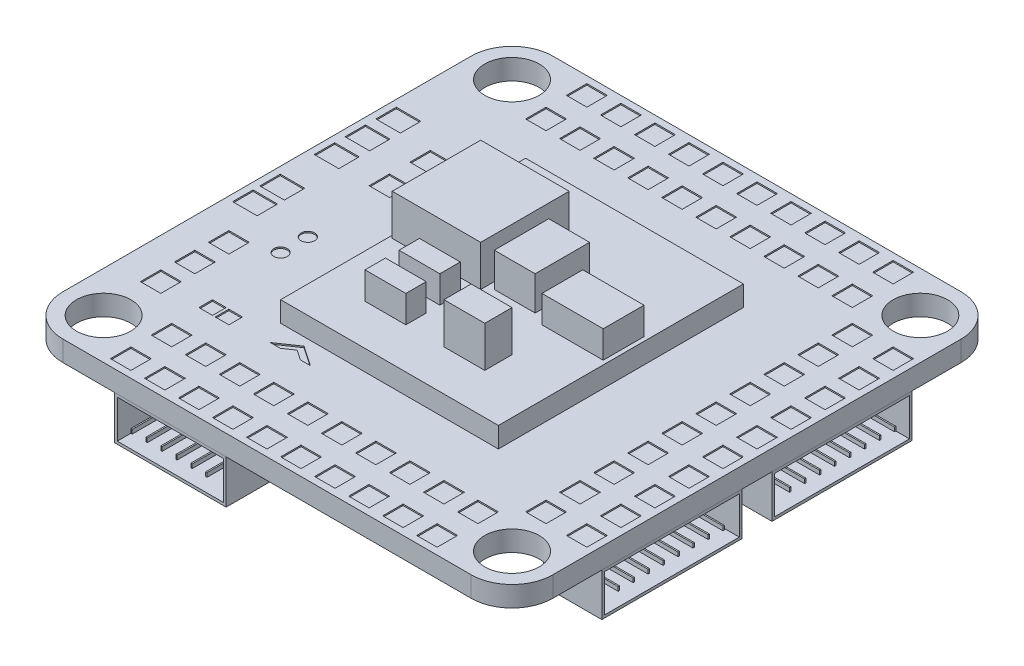
SolidWorks part; units mm, degrees
ref_plane "Front Plane" through (0, 0, 0) normal (0, 0, 1) x (1, 0, 0)
ref_plane "Top Plane" through (0, 0, 0) normal (0, 1, 0) x (1, 0, 0)
ref_plane "Right Plane" through (0, 0, 0) normal (1, 0, 0) x (0, 0, -1)
sketch "Sketch1" plane through (0, 0, 0) normal (0, 1, 0) x (1, 0, 0)
  line L1 (-15, 18) -> (15, 18)
  line L2 (-18, 15) -> (-18, -15)
  line L3 (-15, -18) -> (15, -18)
  line L4 (18, 15) -> (18, -15)
  line L5 (-18, 18) -> (18, -18) construction
  line L6 (-18, -18) -> (18, 18) construction
  circle A0 centre (-15, 15) radius 2
  circle A1 centre (15, 15) radius 2
  circle A2 centre (15, -15) radius 2
  circle A3 centre (-15, -15) radius 2
  arc A4 (-18, -15) -> (-15, -18) centre (-15, -15) ccw
  arc A5 (15, -18) -> (18, -15) centre (15, -15) ccw
  arc A6 (15, 18) -> (18, 15) centre (15, 15) cw
  arc A7 (-18, 15) -> (-15, 18) centre (-15, 15) cw
  point P0 (0, 0)
  dimension "D3" = 4
  dimension "D4" = 3
  dimension "D5" = 3
  dimension "D8" = 30
  dimension "D9" = 30
  dimension "D10" = 3
  dimension "D1" = 36
  dimension "D2" = 36
  dimension "D6" = 2
  dimension "D7" = 2
extrude "Boss-Extrude1" add sketch "Sketch1" along normal blind 1.5
sketch "Sketch2" plane through (0, 1.5, 0) normal (0, 1, 0) x (1, 0, 0)
  line L1 (-8, 9) -> (8, 9)
  line L2 (-8, 9) -> (-8, -9)
  line L3 (-8, -9) -> (8, -9)
  line L4 (8, 9) -> (8, -9)
  line L5 (-8, 9) -> (8, -9) construction
  line L6 (-8, -9) -> (8, 9) construction
  point P0 (0, 0)
  dimension "D1" = 16
  dimension "D2" = 18
extrude "Boss-Extrude2" add sketch "Sketch2" along normal blind 1.5
sketch "Sketch3" plane through (0, 3, 0) normal (0, 1, 0) x (1, 0, 0)
  line L0 (8, 9) -> (-8, 9) construction
  line L1 (-7.8, 5.5) -> (-1.3, 5.5)
  line L2 (-7.8, 5.5) -> (-7.8, -1)
  line L3 (-7.8, -1) -> (-1.3, -1)
  line L4 (-1.3, 5.5) -> (-1.3, -1)
  line L5 (-7.8, 5.5) -> (-1.3, -1) construction
  line L6 (-7.8, -1) -> (-1.3, 5.5) construction
  line L7 (8, -9) -> (8, 9) construction
  point P0 (-4.55, 2.25)
  dimension "D1" = 6.5
  dimension "D2" = 6.5
  dimension "D3" = 3.5
  dimension "D4" = 9.3
extrude "Boss-Extrude3" add sketch "Sketch3" along normal blind 3
sketch "Sketch4" plane through (0, 3, 0) normal (0, 1, 0) x (1, 0, 0)
  line L0 (-7.8, -1) -> (-1.3, -1) construction
  line L1 (-4.8, -2) -> (-1.8, -2)
  line L2 (-4.8, -2) -> (-4.8, -3.5)
  line L3 (-4.8, -3.5) -> (-1.8, -3.5)
  line L4 (-1.8, -2) -> (-1.8, -3.5)
  line L5 (-4.8, -2) -> (-1.8, -3.5) construction
  line L6 (-4.8, -3.5) -> (-1.8, -2) construction
  line L7 (-1.3, -1) -> (-1.3, 5.5) construction
  line L8 (-4.8, -4.5) -> (-4.8, -6)
  line L9 (-4.8, -4.5) -> (-1.8, -4.5)
  line L10 (-1.8, -4.5) -> (-1.8, -6)
  line L11 (-4.8, -6) -> (-1.8, -6)
  point P0 (-3.3, -2.75)
  dimension "D1" = 1.5
  dimension "D2" = 3
  dimension "D3" = 1
  dimension "D4" = 0.5
  dimension "D5" = 2
extrude "Boss-Extrude4" add sketch "Sketch4" along normal blind 2
sketch "Sketch5" plane through (0, 3, 0) normal (0, 1, 0) x (1, 0, 0)
  line L0 (8, -9) -> (8, 9) construction
  line L1 (1, -4) -> (4, -4)
  line L2 (1, -4) -> (1, -6)
  line L3 (1, -6) -> (4, -6)
  line L4 (4, -4) -> (4, -6)
  line L5 (1, -4) -> (4, -6) construction
  line L6 (1, -6) -> (4, -4) construction
  line L7 (-8, -9) -> (8, -9) construction
  point P0 (2.5, -5)
  dimension "D1" = 2
  dimension "D2" = 3
  dimension "D3" = 4
  dimension "D4" = 3
extrude "Boss-Extrude5" add sketch "Sketch5" along normal blind 3
sketch "Sketch6" plane through (0, 3, 0) normal (0, 1, 0) x (1, 0, 0)
  line L0 (-1.3, -1) -> (-1.3, 5.5) construction
  line L1 (-0.8, 3.5) -> (2.2, 3.5)
  line L2 (-0.8, 3.5) -> (-0.8, -0.5)
  line L3 (-0.8, -0.5) -> (2.2, -0.5)
  line L4 (2.2, 3.5) -> (2.2, -0.5)
  line L5 (-0.8, 3.5) -> (2.2, -0.5) construction
  line L6 (-0.8, -0.5) -> (2.2, 3.5) construction
  line L8 (-7.8, -1) -> (-1.3, -1) construction
  point P0 (0.7, 1.5)
  dimension "D1" = 4
  dimension "D2" = 3
  dimension "D3" = 0.5
  dimension "D4" = 0.5
extrude "Boss-Extrude6" add sketch "Sketch6" along normal blind 2.5
sketch "Sketch7" plane through (0, 3, 0) normal (0, 1, 0) x (1, 0, 0)
  line L0 (8, -9) -> (8, 9) construction
  line L1 (3.2, 2) -> (7.7, 2)
  line L2 (3.2, 2) -> (3.2, -1)
  line L3 (3.2, -1) -> (7.7, -1)
  line L4 (7.7, 2) -> (7.7, -1)
  line L5 (3.2, 2) -> (7.7, -1) construction
  line L6 (3.2, -1) -> (7.7, 2) construction
  line L7 (8, 9) -> (-8, 9) construction
  point P0 (5.45, 0.5)
  dimension "D1" = 4.5
  dimension "D2" = 3
  dimension "D3" = 0.3
  dimension "D4" = 7
extrude "Boss-Extrude7" add sketch "Sketch7" along normal blind 2
sketch "Sketch8" plane through (0, 1.5, 0) normal (0, 1, 0) x (1, 0, 0)
  line L0 (-5.6809, -9.5944) -> (-7.1537, -10.6043)
  line L1 (-7.1537, -10.6043) -> (-6.4173, -10.6043)
  line L2 (-6.4173, -10.6043) -> (-5.6809, -10.0993)
  line L3 (-5.6809, -9.5944) -> (-5.6809, -10.6043) construction
  line L4 (-4.9445, -10.6043) -> (-5.6809, -10.0993)
  line L5 (-4.2081, -10.6043) -> (-4.9445, -10.6043)
  line L6 (-5.6809, -9.5944) -> (-4.2081, -10.6043)
extrude "Cut-Extrude1" cut sketch "Sketch8" against normal blind 0.1
sketch "Sketch9" plane through (0, 1.5, 0) normal (0, 1, 0) x (1, 0, 0)
  line L0 (-18, 15) -> (-18, -15) construction
  line L1 (-12, -13) -> (-10.5, -13)
  line L2 (-12, -13) -> (-12, -14.5)
  line L3 (-12, -14.5) -> (-10.5, -14.5)
  line L4 (-10.5, -13) -> (-10.5, -14.5)
  line L5 (-12, -13) -> (-10.5, -14.5) construction
  line L6 (-12, -14.5) -> (-10.5, -13) construction
  line L7 (-15, -18) -> (15, -18) construction
  line L8 (-9.5, -13) -> (-9.5, -14.5)
  line L9 (-9.5, -13) -> (-8, -13)
  line L10 (-8, -13) -> (-8, -14.5)
  line L11 (-9.5, -14.5) -> (-8, -14.5)
  line L12 (-7, -13) -> (-7, -14.5)
  line L13 (-7, -13) -> (-5.5, -13)
  line L14 (-5.5, -13) -> (-5.5, -14.5)
  line L15 (-7, -14.5) -> (-5.5, -14.5)
  line L16 (-4.5, -13) -> (-4.5, -14.5)
  line L17 (-4.5, -13) -> (-3, -13)
  line L18 (-3, -13) -> (-3, -14.5)
  line L19 (-4.5, -14.5) -> (-3, -14.5)
  line L20 (-2, -13) -> (-2, -14.5)
  line L21 (-2, -13) -> (-0.5, -13)
  line L22 (-0.5, -13) -> (-0.5, -14.5)
  line L23 (-2, -14.5) -> (-0.5, -14.5)
  line L24 (0.5, -13) -> (0.5, -14.5)
  line L25 (0.5, -13) -> (2, -13)
  line L26 (2, -13) -> (2, -14.5)
  line L27 (0.5, -14.5) -> (2, -14.5)
  line L28 (3, -13) -> (3, -14.5)
  line L29 (3, -13) -> (4.5, -13)
  line L30 (4.5, -13) -> (4.5, -14.5)
  line L31 (3, -14.5) -> (4.5, -14.5)
  line L32 (5.5, -13) -> (5.5, -14.5)
  line L33 (5.5, -13) -> (7, -13)
  line L34 (7, -13) -> (7, -14.5)
  line L35 (5.5, -14.5) -> (7, -14.5)
  line L36 (8, -13) -> (8, -14.5)
  line L37 (8, -13) -> (9.5, -13)
  line L38 (9.5, -13) -> (9.5, -14.5)
  line L39 (8, -14.5) -> (9.5, -14.5)
  line L40 (10.5, -13) -> (10.5, -14.5)
  line L41 (10.5, -13) -> (12, -13)
  line L42 (12, -13) -> (12, -14.5)
  line L43 (10.5, -14.5) -> (12, -14.5)
  line L44 (-9.5, -16) -> (-9.5, -17.5)
  line L45 (-9.5, -16) -> (-8, -16)
  line L46 (-8, -16) -> (-8, -17.5)
  line L47 (-9.5, -17.5) -> (-8, -17.5)
  line L48 (-7, -16) -> (-7, -17.5)
  line L49 (-7, -16) -> (-5.5, -16)
  line L50 (-5.5, -16) -> (-5.5, -17.5)
  line L51 (-7, -17.5) -> (-5.5, -17.5)
  line L52 (-4.5, -16) -> (-4.5, -17.5)
  line L53 (-4.5, -16) -> (-3, -16)
  line L54 (-3, -16) -> (-3, -17.5)
  line L55 (-4.5, -17.5) -> (-3, -17.5)
  line L56 (-2, -16) -> (-2, -17.5)
  line L57 (-2, -16) -> (-0.5, -16)
  line L58 (-0.5, -16) -> (-0.5, -17.5)
  line L59 (-2, -17.5) -> (-0.5, -17.5)
  line L60 (0.5, -16) -> (0.5, -17.5)
  line L61 (0.5, -16) -> (2, -16)
  line L62 (2, -16) -> (2, -17.5)
  line L63 (0.5, -17.5) -> (2, -17.5)
  line L64 (3, -16) -> (3, -17.5)
  line L65 (3, -16) -> (4.5, -16)
  line L66 (4.5, -16) -> (4.5, -17.5)
  line L67 (3, -17.5) -> (4.5, -17.5)
  line L68 (5.5, -16) -> (5.5, -17.5)
  line L69 (5.5, -16) -> (7, -16)
  line L70 (7, -16) -> (7, -17.5)
  line L71 (5.5, -17.5) -> (7, -17.5)
  line L72 (8, -16) -> (8, -17.5)
  line L73 (8, -16) -> (9.5, -16)
  line L74 (9.5, -16) -> (9.5, -17.5)
  line L75 (8, -17.5) -> (9.5, -17.5)
  line L76 (10.5, -16) -> (10.5, -17.5)
  line L77 (10.5, -16) -> (12, -16)
  line L78 (12, -16) -> (12, -17.5)
  line L79 (10.5, -17.5) -> (12, -17.5)
  line L80 (-12, -16) -> (-12, -17.5)
  line L81 (-12, -16) -> (-10.5, -16)
  line L82 (-10.5, -16) -> (-10.5, -17.5)
  line L83 (-12, -17.5) -> (-10.5, -17.5)
  line L84 (-18, 0) -> (18, 0) construction
  line L85 (18, -15) -> (18, 15) construction
  line L86 (-15, 15) -> (15, -15) construction
  line L87 (14.5, 12) -> (13, 10.5) construction
  line L88 (13, 12) -> (14.5, 10.5) construction
  line L89 (17.5, 12) -> (17.5, 10.5)
  line L90 (16, 10.5) -> (17.5, 10.5)
  line L91 (16, 12) -> (16, 10.5)
  line L92 (16, 12) -> (17.5, 12)
  line L93 (17.5, -10.5) -> (17.5, -12)
  line L94 (16, -12) -> (17.5, -12)
  line L95 (16, -10.5) -> (16, -12)
  line L96 (16, -10.5) -> (17.5, -10.5)
  line L97 (17.5, -8) -> (17.5, -9.5)
  line L98 (16, -9.5) -> (17.5, -9.5)
  line L99 (16, -8) -> (16, -9.5)
  line L100 (16, -8) -> (17.5, -8)
  line L101 (17.5, -5.5) -> (17.5, -7)
  line L102 (16, -7) -> (17.5, -7)
  line L103 (16, -5.5) -> (16, -7)
  line L104 (16, -5.5) -> (17.5, -5.5)
  line L105 (17.5, -3) -> (17.5, -4.5)
  line L106 (16, -4.5) -> (17.5, -4.5)
  line L107 (16, -3) -> (16, -4.5)
  line L108 (16, -3) -> (17.5, -3)
  line L109 (17.5, -0.5) -> (17.5, -2)
  line L110 (16, -2) -> (17.5, -2)
  line L111 (16, -0.5) -> (16, -2)
  line L112 (16, -0.5) -> (17.5, -0.5)
  line L113 (17.5, 2) -> (17.5, 0.5)
  line L114 (16, 0.5) -> (17.5, 0.5)
  line L115 (16, 2) -> (16, 0.5)
  line L116 (16, 2) -> (17.5, 2)
  line L117 (17.5, 4.5) -> (17.5, 3)
  line L118 (16, 3) -> (17.5, 3)
  line L119 (16, 4.5) -> (16, 3)
  line L120 (16, 4.5) -> (17.5, 4.5)
  line L121 (17.5, 7) -> (17.5, 5.5)
  line L122 (16, 5.5) -> (17.5, 5.5)
  line L123 (16, 7) -> (16, 5.5)
  line L124 (16, 7) -> (17.5, 7)
  line L125 (17.5, 9.5) -> (17.5, 8)
  line L126 (16, 8) -> (17.5, 8)
  line L127 (16, 9.5) -> (16, 8)
  line L128 (16, 9.5) -> (17.5, 9.5)
  line L129 (14.5, -10.5) -> (14.5, -12)
  line L130 (13, -12) -> (14.5, -12)
  line L131 (13, -10.5) -> (13, -12)
  line L132 (13, -10.5) -> (14.5, -10.5)
  line L133 (14.5, -8) -> (14.5, -9.5)
  line L134 (13, -9.5) -> (14.5, -9.5)
  line L135 (13, -8) -> (13, -9.5)
  line L136 (13, -8) -> (14.5, -8)
  line L137 (14.5, -5.5) -> (14.5, -7)
  line L138 (13, -7) -> (14.5, -7)
  line L139 (13, -5.5) -> (13, -7)
  line L140 (13, -5.5) -> (14.5, -5.5)
  line L141 (14.5, -3) -> (14.5, -4.5)
  line L142 (13, -4.5) -> (14.5, -4.5)
  line L143 (13, -3) -> (13, -4.5)
  line L144 (13, -3) -> (14.5, -3)
  line L145 (14.5, -0.5) -> (14.5, -2)
  line L146 (13, -2) -> (14.5, -2)
  line L147 (13, -0.5) -> (13, -2)
  line L148 (13, -0.5) -> (14.5, -0.5)
  line L149 (14.5, 2) -> (14.5, 0.5)
  line L150 (13, 0.5) -> (14.5, 0.5)
  line L151 (13, 2) -> (13, 0.5)
  line L152 (13, 2) -> (14.5, 2)
  line L153 (14.5, 4.5) -> (14.5, 3)
  line L154 (13, 3) -> (14.5, 3)
  line L155 (13, 4.5) -> (13, 3)
  line L156 (13, 4.5) -> (14.5, 4.5)
  line L157 (14.5, 7) -> (14.5, 5.5)
  line L158 (13, 5.5) -> (14.5, 5.5)
  line L159 (13, 7) -> (13, 5.5)
  line L160 (13, 7) -> (14.5, 7)
  line L161 (14.5, 9.5) -> (14.5, 8)
  line L162 (13, 8) -> (14.5, 8)
  line L163 (13, 9.5) -> (13, 8)
  line L164 (13, 9.5) -> (14.5, 9.5)
  line L165 (13, 10.5) -> (14.5, 10.5)
  line L166 (14.5, 12) -> (14.5, 10.5)
  line L167 (13, 12) -> (14.5, 12)
  line L168 (13, 12) -> (13, 10.5)
  line L169 (-12, 14.5) -> (-10.5, 13) construction
  line L170 (-12, 13) -> (-10.5, 14.5) construction
  line L171 (-12, 17.5) -> (-10.5, 17.5)
  line L172 (-10.5, 16) -> (-10.5, 17.5)
  line L173 (-12, 16) -> (-10.5, 16)
  line L174 (-12, 16) -> (-12, 17.5)
  line L175 (10.5, 17.5) -> (12, 17.5)
  line L176 (12, 16) -> (12, 17.5)
  line L177 (10.5, 16) -> (12, 16)
  line L178 (10.5, 16) -> (10.5, 17.5)
  line L179 (8, 17.5) -> (9.5, 17.5)
  line L180 (9.5, 16) -> (9.5, 17.5)
  line L181 (8, 16) -> (9.5, 16)
  line L182 (8, 16) -> (8, 17.5)
  line L183 (5.5, 17.5) -> (7, 17.5)
  line L184 (7, 16) -> (7, 17.5)
  line L185 (5.5, 16) -> (7, 16)
  line L186 (5.5, 16) -> (5.5, 17.5)
  line L187 (3, 17.5) -> (4.5, 17.5)
  line L188 (4.5, 16) -> (4.5, 17.5)
  line L189 (3, 16) -> (4.5, 16)
  line L190 (3, 16) -> (3, 17.5)
  line L191 (0.5, 17.5) -> (2, 17.5)
  line L192 (2, 16) -> (2, 17.5)
  line L193 (0.5, 16) -> (2, 16)
  line L194 (0.5, 16) -> (0.5, 17.5)
  line L195 (-2, 17.5) -> (-0.5, 17.5)
  line L196 (-0.5, 16) -> (-0.5, 17.5)
  line L197 (-2, 16) -> (-0.5, 16)
  line L198 (-2, 16) -> (-2, 17.5)
  line L199 (-4.5, 17.5) -> (-3, 17.5)
  line L200 (-3, 16) -> (-3, 17.5)
  line L201 (-4.5, 16) -> (-3, 16)
  line L202 (-4.5, 16) -> (-4.5, 17.5)
  line L203 (-7, 17.5) -> (-5.5, 17.5)
  line L204 (-5.5, 16) -> (-5.5, 17.5)
  line L205 (-7, 16) -> (-5.5, 16)
  line L206 (-7, 16) -> (-7, 17.5)
  line L207 (-9.5, 17.5) -> (-8, 17.5)
  line L208 (-8, 16) -> (-8, 17.5)
  line L209 (-9.5, 16) -> (-8, 16)
  line L210 (-9.5, 16) -> (-9.5, 17.5)
  line L211 (10.5, 14.5) -> (12, 14.5)
  line L212 (12, 13) -> (12, 14.5)
  line L213 (10.5, 13) -> (12, 13)
  line L214 (10.5, 13) -> (10.5, 14.5)
  line L215 (8, 14.5) -> (9.5, 14.5)
  line L216 (9.5, 13) -> (9.5, 14.5)
  line L217 (8, 13) -> (9.5, 13)
  line L218 (8, 13) -> (8, 14.5)
  line L219 (5.5, 14.5) -> (7, 14.5)
  line L220 (7, 13) -> (7, 14.5)
  line L221 (5.5, 13) -> (7, 13)
  line L222 (5.5, 13) -> (5.5, 14.5)
  line L223 (3, 14.5) -> (4.5, 14.5)
  line L224 (4.5, 13) -> (4.5, 14.5)
  line L225 (3, 13) -> (4.5, 13)
  line L226 (3, 13) -> (3, 14.5)
  line L227 (0.5, 14.5) -> (2, 14.5)
  line L228 (2, 13) -> (2, 14.5)
  line L229 (0.5, 13) -> (2, 13)
  line L230 (0.5, 13) -> (0.5, 14.5)
  line L231 (-2, 14.5) -> (-0.5, 14.5)
  line L232 (-0.5, 13) -> (-0.5, 14.5)
  line L233 (-2, 13) -> (-0.5, 13)
  line L234 (-2, 13) -> (-2, 14.5)
  line L235 (-4.5, 14.5) -> (-3, 14.5)
  line L236 (-3, 13) -> (-3, 14.5)
  line L237 (-4.5, 13) -> (-3, 13)
  line L238 (-4.5, 13) -> (-4.5, 14.5)
  line L239 (-7, 14.5) -> (-5.5, 14.5)
  line L240 (-5.5, 13) -> (-5.5, 14.5)
  line L241 (-7, 13) -> (-5.5, 13)
  line L242 (-7, 13) -> (-7, 14.5)
  line L243 (-9.5, 14.5) -> (-8, 14.5)
  line L244 (-8, 13) -> (-8, 14.5)
  line L245 (-9.5, 13) -> (-8, 13)
  line L246 (-9.5, 13) -> (-9.5, 14.5)
  line L247 (-10.5, 13) -> (-10.5, 14.5)
  line L248 (-12, 14.5) -> (-10.5, 14.5)
  line L249 (-12, 13) -> (-12, 14.5)
  line L250 (-12, 13) -> (-10.5, 13)
  line L251 (-10.8, -10) -> (-10.8, -11)
  line L252 (-12, -10) -> (-11, -10)
  line L253 (-12, -10) -> (-12, -11)
  line L254 (-12, -11) -> (-11, -11)
  line L255 (-11, -10) -> (-11, -11)
  line L256 (-12, -10) -> (-11, -11) construction
  line L257 (-12, -11) -> (-11, -10) construction
  line L258 (-10.8, -10) -> (-9.8, -10)
  line L259 (-9.8, -10) -> (-9.8, -11)
  line L260 (-10.8, -11) -> (-9.8, -11)
  line L261 (-10.5, -16) -> (-12, -17.5) construction
  line L262 (-8, -13) -> (-9.5, -14.5) construction
  line L263 (-8, -16) -> (-9.5, -17.5) construction
  line L264 (-12, -16) -> (-10.5, -17.5) construction
  line L265 (-9.5, -16) -> (-8, -17.5) construction
  line L266 (-9.5, -13) -> (-8, -14.5) construction
  line L267 (-10.8, -10) -> (-9.8, -11) construction
  line L268 (-9.8, -10) -> (-10.8, -11) construction
  line L269 (-7, -13) -> (-5.5, -14.5) construction
  line L270 (-5.5, -16) -> (-7, -17.5) construction
  line L271 (-4.5, -14.5) -> (-3, -13) construction
  line L272 (15, 18) -> (-15, 18) construction
  line L273 (-15.7, 9) -> (-17.5, 9)
  line L274 (-15.7, 9) -> (-15.7, 7.5)
  line L275 (-15.7, 7.5) -> (-17.5, 7.5)
  line L276 (-17.5, 9) -> (-17.5, 7.5)
  line L277 (-15.7, 9) -> (-17.5, 7.5) construction
  line L278 (-15.7, 7.5) -> (-17.5, 9) construction
  line L279 (-15.7, 6.7373) -> (-15.7, 5.2373)
  line L280 (-15.7, 6.7373) -> (-17.5, 6.7373)
  line L281 (-17.5, 6.7373) -> (-17.5, 5.2373)
  line L282 (-15.7, 5.2373) -> (-17.5, 5.2373)
  line L283 (-15.7, 4.4745) -> (-15.7, 2.9745)
  line L284 (-15.7, 4.4745) -> (-17.5, 4.4745)
  line L285 (-17.5, 4.4745) -> (-17.5, 2.9745)
  line L286 (-15.7, 2.9745) -> (-17.5, 2.9745)
  line L287 (-15.7, -1.5255) -> (-15.7, -3.0255)
  line L288 (-15.7, 0.4745) -> (-17.5, 0.4745)
  line L289 (-15.7, 0.4745) -> (-15.7, -1.0255)
  line L290 (-15.7, -1.0255) -> (-17.5, -1.0255)
  line L291 (-17.5, 0.4745) -> (-17.5, -1.0255)
  line L292 (-15.7, 0.4745) -> (-17.5, -1.0255) construction
  line L293 (-15.7, -1.0255) -> (-17.5, 0.4745) construction
  line L294 (-15.7, -1.5255) -> (-17.5, -1.5255)
  line L295 (-17.5, -1.5255) -> (-17.5, -3.0255)
  line L296 (-15.7, -3.0255) -> (-17.5, -3.0255)
  line L297 (-12, 4.5) -> (-12, 3)
  line L298 (-12, 7.5) -> (-13.5, 7.5)
  line L299 (-12, 7.5) -> (-12, 6)
  line L300 (-12, 6) -> (-13.5, 6)
  line L301 (-13.5, 7.5) -> (-13.5, 6)
  line L302 (-12, 7.5) -> (-13.5, 6) construction
  line L303 (-12, 6) -> (-13.5, 7.5) construction
  line L304 (-12, 4.5) -> (-13.5, 4.5)
  line L305 (-13.5, 4.5) -> (-13.5, 3)
  line L306 (-12, 3) -> (-13.5, 3)
  line L307 (-14.3, -7.5) -> (-14.3, -9)
  line L308 (-14.3, -10) -> (-15.8, -10)
  line L309 (-14.3, -10) -> (-14.3, -11.5)
  line L310 (-14.3, -11.5) -> (-15.8, -11.5)
  line L311 (-15.8, -10) -> (-15.8, -11.5)
  line L312 (-14.3, -10) -> (-15.8, -11.5) construction
  line L313 (-14.3, -11.5) -> (-15.8, -10) construction
  line L314 (-14.3, -7.5) -> (-15.8, -7.5)
  line L315 (-15.8, -7.5) -> (-15.8, -9)
  line L316 (-14.3, -9) -> (-15.8, -9)
  line L317 (-14.3, -5) -> (-14.3, -6.5)
  line L318 (-14.3, -5) -> (-15.8, -5)
  line L319 (-15.8, -5) -> (-15.8, -6.5)
  line L320 (-14.3, -6.5) -> (-15.8, -6.5)
  circle A0 centre (-12.5, -4.5) radius 0.5
  circle A1 centre (-12.5, -2.5) radius 0.5
  point P0 (-11.25, -13.75)
  point P173 (13.75, 11.25)
  point P254 (-11.25, 13.75)
  point P255 (-11.5, -10.5)
  point P260 (-16.6, 8.25)
  point P271 (-16.6, -0.2755)
  point P284 (-12.75, 6.75)
  point P293 (-15.05, -10.75)
  dimension "D32" = 1
  dimension "D33" = 5.5
  dimension "D34" = 13.5
  dimension "D1" = 1.5
  dimension "D2" = 1.5
  dimension "D3" = 6
  dimension "D4" = 3.5
  dimension "D7" = 1
  dimension "D8" = 1
  dimension "D9" = 0
  dimension "D10" = 2
  dimension "D12" = 9
  dimension "D13" = 1.5
  dimension "D14" = 1.8
  dimension "D16" = 1.5
  dimension "D17" = 1.8
  dimension "D18" = 2.5
  dimension "D19" = 0.5
  dimension "D20" = 0.5
  dimension "D22" = 1.5
  dimension "D23" = 1.5
  dimension "D24" = 4.5
  dimension "D25" = 10.5
  dimension "D27" = 1.5
  dimension "D28" = 1.5
  dimension "D29" = 6.5
  dimension "D30" = 2.2
  dimension "D5" = 10
  dimension "D6" = 2
  dimension "D11" = 2
  dimension "D15" = 3
  dimension "D21" = 2
  dimension "D26" = 2
  dimension "D31" = 3
  dimension "D35" = 2
extrude "Cut-Extrude2" cut sketch "Sketch9" against normal blind 0.1
sketch "Sketch12" plane through (-18, 0, 0) normal (-1, 0, 0) x (0, 0, 1)
  line L1 (-8.7, 0) -> (-3.1, 0)
  line L3 (-8.7, -3.2) -> (-3.1, -3.2)
  line L6 (-18, 1.5) -> (-18, 0) construction
  line L7 (-15, 0) -> (15, 0) construction
  arc A0 (-3.1, 0) -> (-3.1, -3.2) centre (-3.1, -1.6) cw
  arc A1 (-8.7, -3.2) -> (-8.7, 0) centre (-8.7, -1.6) cw
  point P1 (0, 0)
  dimension "D1" = 1.6
  dimension "D2" = 1.6
  dimension "D3" = 9.3
  dimension "D6" = 5.6
  dimension "D4" = 5.6
  dimension "D5" = 3.2
  dimension "D7" = 3.2
extrude "Boss-Extrude8" add sketch "Sketch12" along normal blind 1.5 and the other way blind 5.7
sketch "Sketch13" plane through (-19.5, 0, 0) normal (-1, 0, 0) x (0, 0, 1)
  line L0 (-3.1, 0) -> (-8.7, 0) construction
  line L1 (-8.7, 0) -> (-3.1, 0)
  line L2 (-3.1, -3.2) -> (-8.7, -3.2)
  line L3 (-3.1, -3.1) -> (-8.7, -3.1)
  line L4 (-8.7, -0.1) -> (-3.1, -0.1)
  line L5 (-8.7, -1.6) -> (-3.1, -1.6) construction
  line L6 (-8.7, -1.8) -> (-3.1, -1.8)
  line L7 (-8.7, -1.4) -> (-3.1, -1.4)
  arc A0 (-8.7, -3.2) -> (-8.7, 0) centre (-8.7, -1.6) cw
  arc A1 (-3.1, 0) -> (-3.1, -3.2) centre (-3.1, -1.6) cw
  arc A2 (-3.1, -3.2) -> (-3.1, 0) centre (-3.1, -1.6) ccw construction
  arc A3 (-8.7, -3.1) -> (-8.7, -0.1) centre (-8.7, -1.6) cw
  arc A4 (-3.1, -0.1) -> (-3.1, -3.1) centre (-3.1, -1.6) cw
  arc A5 (-3.1, -1.4) -> (-3.1, -1.8) centre (-3.1, -1.6) cw
  arc A6 (-8.7, -1.8) -> (-8.7, -1.4) centre (-8.7, -1.6) cw
  dimension "D1" = 0.1
  dimension "D2" = 0.2
  dimension "D3" = 0.2
extrude "Cut-Extrude3" cut sketch "Sketch13" against normal blind 6 contours A4 L4 A3 L3 L6 A6 L7 A5
sketch "Sketch15" plane through (0, 0, 0) normal (0, -1, 0) x (1, 0, 0)
  line L1 (-17.7, 5) -> (-15.2, 5)
  line L2 (-17.7, 5) -> (-17.7, 9.5)
  line L3 (-17.7, 9.5) -> (-15.2, 9.5)
  line L4 (-15.2, 5) -> (-15.2, 9.5)
  line L5 (-17.7, 5) -> (-15.2, 9.5) construction
  line L6 (-17.7, 9.5) -> (-15.2, 5) construction
  line L8 (-12.3, -1.5) -> (-19.5, -1.5) construction
  line L9 (-18, -3.1) -> (-18, 15) construction
  point P0 (-16.45, 7.25)
  dimension "D1" = 6.5
  dimension "D2" = 2.8
  dimension "D3" = 2.5
  dimension "D4" = 4.5
extrude "Boss-Extrude9" add sketch "Sketch15" along normal blind 2
sketch "Sketch16" plane through (-17.7, 0, 0) normal (-1, 0, 0) x (0, 0, 1)
  line L0 (5, 0) -> (9.5, -2) construction
  line L1 (9.5, 0) -> (5, -2) construction
  line L3 (6.25, -0.5) -> (8.25, -0.5)
  line L4 (6.25, -0.5) -> (6.25, -1.5)
  line L5 (6.25, -1.5) -> (8.25, -1.5)
  line L6 (8.25, -0.5) -> (8.25, -1.5)
  line L7 (6.25, -0.5) -> (8.25, -1.5) construction
  line L8 (6.25, -1.5) -> (8.25, -0.5) construction
  point P8 (7.25, -1)
  dimension "D1" = 2
  dimension "D2" = 1
extrude "Boss-Extrude10" add sketch "Sketch16" along normal blind 1
sketch "Sketch17" plane through (0, 0, 18) normal (0, 0, 1) x (1, 0, 0)
  line L0 (-15, 0) -> (15, 0) construction
  line L1 (-11.2, 0) -> (-3, 0)
  line L2 (-11.2, 0) -> (-11.2, -3.2)
  line L3 (-11.2, -3.2) -> (-3, -3.2)
  line L4 (-3, 0) -> (-3, -3.2)
  line L5 (-18, 1.5) -> (-18, 0) construction
  dimension "D1" = 15
  dimension "D2" = 8.2
  dimension "D3" = 3.2
extrude "Boss-Extrude11" add sketch "Sketch17" against normal blind 4.5 separate body
sketch "Sketch18" plane through (0, 0, 18) normal (0, 0, 1) x (1, 0, 0)
  line L0 (-11.2, 0) -> (-11.2, -3.2)
  line L1 (-11.2, -3.2) -> (-3, -3.2)
  line L2 (-3, -3.2) -> (-3, 0)
  line L3 (-3, 0) -> (-11.2, 0)
  line L4 (-3.2, -0.2) -> (-11, -0.2)
  line L5 (-11, -0.2) -> (-11, -3)
  line L6 (-11, -3) -> (-3.2, -3)
  line L7 (-3.2, -3) -> (-3.2, -0.2)
  line L8 (-8.9, -1.7) -> (-8.9, -2)
  line L9 (-10, -1.7) -> (-9.9, -1.7)
  line L10 (-10, -1.7) -> (-10, -2)
  line L11 (-10, -2) -> (-9.9, -2)
  line L12 (-9.9, -1.7) -> (-9.9, -2)
  line L13 (-10, -1.7) -> (-9.9, -2) construction
  line L14 (-10, -2) -> (-9.9, -1.7) construction
  line L15 (-8.9, -1.7) -> (-8.8, -1.7)
  line L16 (-8.8, -1.7) -> (-8.8, -2)
  line L17 (-8.9, -2) -> (-8.8, -2)
  line L18 (-7.8, -1.7) -> (-7.8, -2)
  line L19 (-7.8, -1.7) -> (-7.7, -1.7)
  line L20 (-7.7, -1.7) -> (-7.7, -2)
  line L21 (-7.8, -2) -> (-7.7, -2)
  line L22 (-6.7, -1.7) -> (-6.7, -2)
  line L23 (-6.7, -1.7) -> (-6.6, -1.7)
  line L24 (-6.6, -1.7) -> (-6.6, -2)
  line L25 (-6.7, -2) -> (-6.6, -2)
  line L26 (-5.6, -1.7) -> (-5.6, -2)
  line L27 (-5.6, -1.7) -> (-5.5, -1.7)
  line L28 (-5.5, -1.7) -> (-5.5, -2)
  line L29 (-5.6, -2) -> (-5.5, -2)
  line L30 (-4.5, -1.7) -> (-4.5, -2)
  line L31 (-4.5, -1.7) -> (-4.4, -1.7)
  line L32 (-4.4, -1.7) -> (-4.4, -2)
  line L33 (-4.5, -2) -> (-4.4, -2)
  point P12 (-9.95, -1.85)
  point P17 (-9.95, -2)
  dimension "D2" = 0.1
  dimension "D3" = 0.3
  dimension "D4" = 1
  dimension "D5" = 1
  dimension "D1" = 0.2
  dimension "D6" = 6
extrude "Cut-Extrude4" cut sketch "Sketch18" against normal blind 4 contours L6 L7 L4 L5 L33 L30 L31 L32 L29 L26 L27 L28 L25 L22 L23 L24 L21 L18 L19 L20 L17 L8 L15 L16 L9 L12 L11 L10
sketch "Sketch19" plane through (18, 0, 0) normal (1, 0, 0) x (0, 0, -1)
  line L0 (-15, 0) -> (15, 0) construction
  line L1 (-11.4, 0) -> (-1.1, 0)
  line L2 (-11.4, 0) -> (-11.4, -3.1558)
  line L3 (-11.4, -3.1558) -> (-1.1, -3.1558)
  line L4 (-1.1, 0) -> (-1.1, -3.1558)
  line L5 (-18, 1.5) -> (-18, 0) construction
  line L6 (0, 0) -> (0, -3.1558) construction
  line L7 (1.1, 0) -> (1.1, -3.1558)
  line L8 (11.4, -3.1558) -> (1.1, -3.1558)
  line L9 (11.4, 0) -> (11.4, -3.1558)
  line L10 (11.4, 0) -> (1.1, 0)
  dimension "D1" = 10.3
  dimension "D2" = 6.6
extrude "Boss-Extrude12" add sketch "Sketch19" against normal blind 4.3 separate body
sketch "Sketch20" plane through (18, 0, 0) normal (1, 0, 0) x (0, 0, -1)
  line L0 (-11.2, -0.2) -> (-11.2, -2.9558)
  line L1 (-11.4, 0) -> (-1.1, 0)
  line L2 (-11.4, 0) -> (-11.4, -3.1558)
  line L3 (-11.4, -3.1558) -> (-1.1, -3.1558)
  line L4 (-1.1, 0) -> (-1.1, -3.1558)
  line L5 (1.1, 0) -> (11.4, 0)
  line L6 (1.1, 0) -> (1.1, -3.1558)
  line L7 (1.1, -3.1558) -> (11.4, -3.1558)
  line L8 (11.4, 0) -> (11.4, -3.1558)
  line L9 (-11.2, -2.9558) -> (-1.3, -2.9558)
  line L10 (-1.3, -0.2) -> (-1.3, -2.9558)
  line L11 (-11.2, -0.2) -> (-1.3, -0.2)
  line L12 (1.3, -0.2) -> (1.3, -2.9558)
  line L13 (1.3, -2.9558) -> (11.2, -2.9558)
  line L14 (11.2, -0.2) -> (11.2, -2.9558)
  line L15 (1.3, -0.2) -> (11.2, -0.2)
  line L16 (0, 0) -> (0, -3.1558) construction
  line L17 (-10.2, -1.6558) -> (-10.1, -1.6558)
  line L18 (-10.2, -1.6558) -> (-10.2, -1.9558)
  line L19 (-10.2, -1.9558) -> (-10.1, -1.9558)
  line L20 (-10.1, -1.6558) -> (-10.1, -1.9558)
  line L21 (-10.2, -1.6558) -> (-10.1, -1.9558) construction
  line L22 (-10.2, -1.9558) -> (-10.1, -1.6558) construction
  line L23 (-9.1, -1.6558) -> (-9.1, -1.9558)
  line L24 (-9.1, -1.6558) -> (-9, -1.6558)
  line L25 (-9, -1.6558) -> (-9, -1.9558)
  line L26 (-9.1, -1.9558) -> (-9, -1.9558)
  line L27 (-8, -1.6558) -> (-8, -1.9558)
  line L28 (-8, -1.6558) -> (-7.9, -1.6558)
  line L29 (-7.9, -1.6558) -> (-7.9, -1.9558)
  line L30 (-8, -1.9558) -> (-7.9, -1.9558)
  line L31 (-6.9, -1.6558) -> (-6.9, -1.9558)
  line L32 (-6.9, -1.6558) -> (-6.8, -1.6558)
  line L33 (-6.8, -1.6558) -> (-6.8, -1.9558)
  line L34 (-6.9, -1.9558) -> (-6.8, -1.9558)
  line L35 (-5.8, -1.6558) -> (-5.8, -1.9558)
  line L36 (-5.8, -1.6558) -> (-5.7, -1.6558)
  line L37 (-5.7, -1.6558) -> (-5.7, -1.9558)
  line L38 (-5.8, -1.9558) -> (-5.7, -1.9558)
  line L39 (-4.7, -1.6558) -> (-4.7, -1.9558)
  line L40 (-4.7, -1.6558) -> (-4.6, -1.6558)
  line L41 (-4.6, -1.6558) -> (-4.6, -1.9558)
  line L42 (-4.7, -1.9558) -> (-4.6, -1.9558)
  line L43 (-3.6, -1.6558) -> (-3.6, -1.9558)
  line L44 (-3.6, -1.6558) -> (-3.5, -1.6558)
  line L45 (-3.5, -1.6558) -> (-3.5, -1.9558)
  line L46 (-3.6, -1.9558) -> (-3.5, -1.9558)
  line L47 (-2.5, -1.6558) -> (-2.5, -1.9558)
  line L48 (-2.5, -1.6558) -> (-2.4, -1.6558)
  line L49 (-2.4, -1.6558) -> (-2.4, -1.9558)
  line L50 (-2.5, -1.9558) -> (-2.4, -1.9558)
  line L51 (10.2, -1.9558) -> (10.1, -1.6558) construction
  line L52 (10.2, -1.6558) -> (10.1, -1.9558) construction
  line L53 (2.5, -1.9558) -> (2.4, -1.9558)
  line L54 (2.4, -1.6558) -> (2.4, -1.9558)
  line L55 (2.5, -1.6558) -> (2.4, -1.6558)
  line L56 (2.5, -1.6558) -> (2.5, -1.9558)
  line L57 (3.6, -1.9558) -> (3.5, -1.9558)
  line L58 (3.5, -1.6558) -> (3.5, -1.9558)
  line L59 (3.6, -1.6558) -> (3.5, -1.6558)
  line L60 (3.6, -1.6558) -> (3.6, -1.9558)
  line L61 (4.7, -1.9558) -> (4.6, -1.9558)
  line L62 (4.6, -1.6558) -> (4.6, -1.9558)
  line L63 (4.7, -1.6558) -> (4.6, -1.6558)
  line L64 (4.7, -1.6558) -> (4.7, -1.9558)
  line L65 (5.8, -1.9558) -> (5.7, -1.9558)
  line L66 (5.7, -1.6558) -> (5.7, -1.9558)
  line L67 (5.8, -1.6558) -> (5.7, -1.6558)
  line L68 (5.8, -1.6558) -> (5.8, -1.9558)
  line L69 (6.9, -1.9558) -> (6.8, -1.9558)
  line L70 (6.8, -1.6558) -> (6.8, -1.9558)
  line L71 (6.9, -1.6558) -> (6.8, -1.6558)
  line L72 (6.9, -1.6558) -> (6.9, -1.9558)
  line L73 (8, -1.9558) -> (7.9, -1.9558)
  line L74 (7.9, -1.6558) -> (7.9, -1.9558)
  line L75 (8, -1.6558) -> (7.9, -1.6558)
  line L76 (8, -1.6558) -> (8, -1.9558)
  line L77 (9.1, -1.9558) -> (9, -1.9558)
  line L78 (9, -1.6558) -> (9, -1.9558)
  line L79 (9.1, -1.6558) -> (9, -1.6558)
  line L80 (9.1, -1.6558) -> (9.1, -1.9558)
  line L81 (10.1, -1.6558) -> (10.1, -1.9558)
  line L82 (10.2, -1.9558) -> (10.1, -1.9558)
  line L83 (10.2, -1.6558) -> (10.2, -1.9558)
  line L84 (10.2, -1.6558) -> (10.1, -1.6558)
  point P20 (-10.15, -1.8058)
  point P88 (10.15, -1.8058)
  dimension "D3" = 0.1
  dimension "D4" = 0.3
  dimension "D5" = 1
  dimension "D6" = 1
  dimension "D1" = 0.2
  dimension "D2" = 0.2
  dimension "D7" = 8
extrude "Cut-Extrude5" cut sketch "Sketch20" against normal blind 3.5 contours L11 L0 L9 L10 L50 L47 L48 L49 L46 L43 L44 L45 L42 L39 L40 L41 L38 L35 L36 L37 L34 L31 L32 L33 L30 L27 L28 L29 L26 L23 L24 L25 L17 L20 L19 L18 | L15 L12 L13 L14 L84 L83 L82 L81 L55 L56 L53 L54 L59 L60 L57 L58 L63 L64 L61 L62 L67 L68 L65 L66 L71 L72 L69 L70 L75 L76 L73 L74 L79 L80 L77 L78
